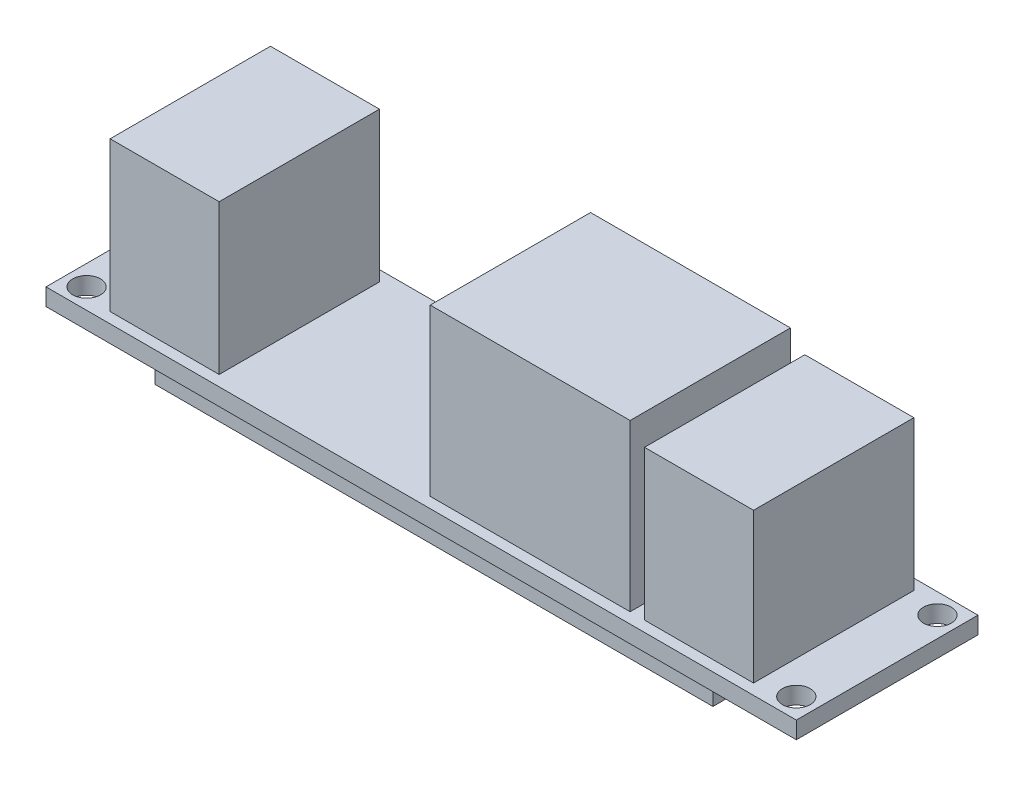
SolidWorks part; units mm, degrees
ref_plane "Front Plane" through (0, 0, 0) normal (0, 0, 1) x (1, 0, 0)
ref_plane "Top Plane" through (0, 0, 0) normal (0, 1, 0) x (1, 0, 0)
ref_plane "Right Plane" through (0, 0, 0) normal (1, 0, 0) x (0, 0, -1)
sketch "Sketch1" plane through (0, 0, 0) normal (0, 1, 0) x (1, 0, 0)
  line L0 (-35.1, 0) -> (0, 0) construction
  line L1 (-35.1, -8.5) -> (35.1, -8.5)
  line L2 (-35.1, -8.5) -> (-35.1, 8.5)
  line L3 (-35.1, 8.5) -> (35.1, 8.5)
  line L4 (35.1, -8.5) -> (35.1, 8.5)
  line L5 (-35.1, -8.5) -> (35.1, 8.5) construction
  line L6 (-35.1, 8.5) -> (35.1, -8.5) construction
  line L7 (0, 0) -> (0, 8.5) construction
  circle A0 centre (-33.2, 6.6) radius 1.3
  circle A1 centre (33.2, 6.6) radius 1.3
  circle A2 centre (33.2, -6.6) radius 1.3
  circle A3 centre (-33.2, -6.6) radius 1.3
  point P0 (0, 0)
  point P8 (-33.2, 7.9)
  point P9 (-34.5, 6.6)
  dimension "D3" = 2.6
  dimension "D1" = 70.2
  dimension "D2" = 17
  dimension "D4" = 0.6
  dimension "D5" = 0.6
extrude "Boss-Extrude1" add sketch "Sketch1" against normal blind 1.6
sketch "Sketch2" plane through (0, 0, 0) normal (0, 0, 1) x (1, 0, 0)
  line L0 (-35.1, 0) -> (35.1, 0) construction
  line L1 (-0.15, 0) -> (18.55, 0)
  line L2 (-0.15, 0) -> (-0.15, 15.5)
  line L3 (-0.15, 15.5) -> (18.55, 15.5)
  line L4 (18.55, 0) -> (18.55, 15.5)
  line L5 (35.1, -1.6) -> (35.1, 0) construction
  line L6 (19.9, 0) -> (30.1, 0)
  line L7 (19.9, 0) -> (19.9, 14)
  line L8 (19.9, 14) -> (30.1, 14)
  line L9 (30.1, 0) -> (30.1, 14)
  line L10 (-30.1, 0) -> (-19.9, 0)
  line L11 (-30.1, 0) -> (-30.1, 14)
  line L12 (-30.1, 14) -> (-19.9, 14)
  line L13 (-19.9, 0) -> (-19.9, 14)
  line L14 (-35.1, -1.6) -> (-35.1, 0) construction
  point P16 (35.1, -0.8)
  dimension "D1" = 10.2
  dimension "D2" = 18.7
  dimension "D3" = 1.35
  dimension "D4" = 5
  dimension "D5" = 5
  dimension "D6" = 14
  dimension "D7" = 15.5
extrude "Boss-Extrude2" add sketch "Sketch2" along normal mid plane 15
sketch "Sketch3" plane through (0, -1.6, 0) normal (0, -1, 0) x (1, 0, 0)
  line L0 (35.1, 8.5) -> (35.1, -8.5) construction
  line L1 (-26.1, -7.3035) -> (26.1, -7.3035)
  line L2 (-26.1, -7.3035) -> (-26.1, 7.3035)
  line L3 (-26.1, 7.3035) -> (26.1, 7.3035)
  line L4 (26.1, -7.3035) -> (26.1, 7.3035)
  line L5 (-26.1, -7.3035) -> (26.1, 7.3035) construction
  line L6 (-26.1, 7.3035) -> (26.1, -7.3035) construction
  point P0 (0, 0)
  dimension "D1" = 9
extrude "Boss-Extrude3" add sketch "Sketch3" along normal blind 2.4
